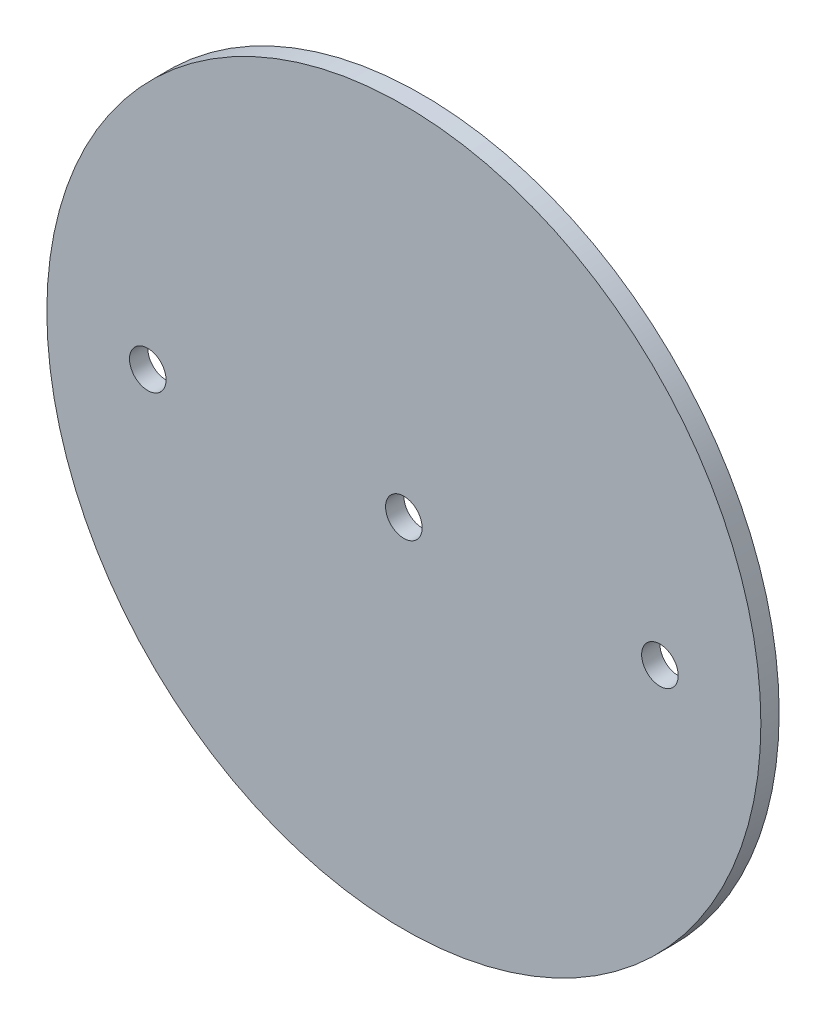
SolidWorks part; units mm, degrees
ref_plane "Front Plane" through (0, 0, 0) normal (0, 0, 1) x (1, 0, 0)
ref_plane "Top Plane" through (0, 0, 0) normal (0, 1, 0) x (1, 0, 0)
ref_plane "Right Plane" through (0, 0, 0) normal (1, 0, 0) x (0, 0, -1)
sketch "Sketch1" plane through (0, 0, 0) normal (0, 0, 1) x (1, 0, 0)
  circle A0 centre (0, 0) radius 61.976
  dimension "D1" = 123.952
extrude "Boss-Extrude1" add sketch "Sketch1" along normal mid plane 3.175
sketch "Sketch2" plane through (0, 0, 1.5875) normal (0, 0, 1) x (1, 0, 0)
  line L0 (-1000, 0) -> (49000, 0) construction
  point P1 (0, 0)
  point P4 (44.45, 0)
  point P5 (-44.45, 0)
  dimension "D1" = 44.45
  dimension "D2" = 88.9
hole_wizard "1/4 (0.25) Diameter Hole1" positions "Sketch2" profile "Sketch3" hole size "1/4" standard "ANSI Inch" end condition through all
sketch "Sketch3" plane through (-44.45, 0, 1.5875) normal (1, 0, 0) x (0, -1, 0)
  line L0 (0, 0) -> (0, 3.175)
  line L1 (0, 3.175) -> (3.175, 3.175)
  line L2 (3.175, 3.175) -> (3.175, 0)
  line L5 (3.175, 0) -> (0, 0)
  line L11 (0, -6.35) -> (0, 107.95) construction
  dimension "Thru Hole Dia." = 6.35
  dimension "Thru Hole Depth" = 3.175
equation "\"AIRFRAME_OD\"= 5.15in"
equation "\"AIRFRAME_ID\"= 5.00in"
equation "\"FLAT_T\"= 0.125in"
equation "\"NOSE_EXP_L\"= 27in"
equation "\"NOSE_SHOULDER_L\"= 5in"
equation "\"MAIN_L\"= 30in"
equation "\"RECO_COUP_L\"= 10in"
equation "\"RECO_SWITCH_L\"= 2in"
equation "\"DROGUE_L\"= 20in"
equation "\"ATS_FORE_COUP_L\"= 5.5in"
equation "\"ATS_AFT_COUP_L\"= 4.5in"
equation "\"LOWER_L\"= 30in"
equation "\"FIN_N\"= 4"
equation "\"CR_AFT_X\"= 0.5in"
equation "\"CR_FORE_X\"= 9.25in"
equation "\"FIN_ROOT\"= 8in"
equation "\"FIN_X\"= 0.75in"
equation "\"MOTOR_OD\"= 3.091in"
equation "\"MOTOR_ID\"= 3.00in"
equation "\"COUPLER_OD\"= 4.998in"
equation "\"COUPLER_ID\"= 4.88in"
equation "\"D1@Sketch1\"=\"COUPLER_ID\""
equation "\"D1@Boss-Extrude1\"=\"FLAT_T\""
equation "\"RECO_ROD_X\"= 3.5in"
equation "\"ATS_ROD_X\"= 3in"
equation "\"D1@Sketch2\"=\"RECO_ROD_X\"*0.5"
equation "\"D2@Sketch2\"=\"RECO_ROD_X\""
equation "\"MOTOR_L\"= 14in"
equation "\"MOTOR_LOWER_X\"= 2in"
